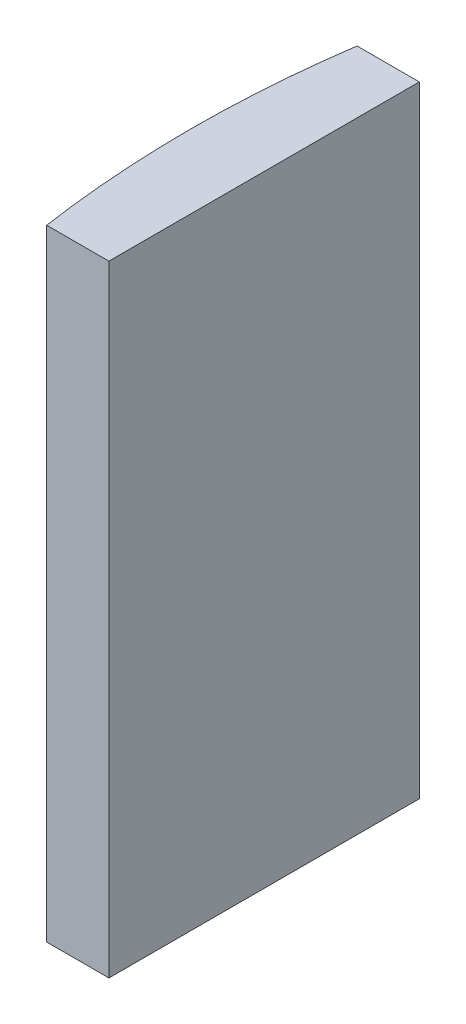
SolidWorks part; units mm, degrees
ref_plane "前视基准面" through (0, 0, 0) normal (0, 0, 1) x (1, 0, 0)
ref_plane "上视基准面" through (0, 0, 0) normal (0, 1, 0) x (1, 0, 0)
ref_plane "右视基准面" through (0, 0, 0) normal (1, 0, 0) x (0, 0, -1)
sketch "草图1" plane through (0, 0, 0) normal (0, 1, 0) x (1, 0, 0)
  line L0 (-137.6835, 0) -> (10.8051, 0) construction
  line L1 (-29.6289, 5) -> (-27.6248, 5)
  line L2 (-29.6289, -5) -> (-27.6248, -5)
  line L3 (-27.6248, 5) -> (-27.6248, -5)
  arc A0 (-29.6289, 5) -> (-29.6289, -5) centre (4.3552, 0) ccw
  point P2 (-29.9948, 0)
  point P4 (-27.6248, 0)
  dimension "D2" = 5
  dimension "D3" = 34.35
  dimension "D4" = 2.37
  dimension "D1" = 5
extrude "凸台-拉伸1" add sketch "草图1" along normal blind 20
